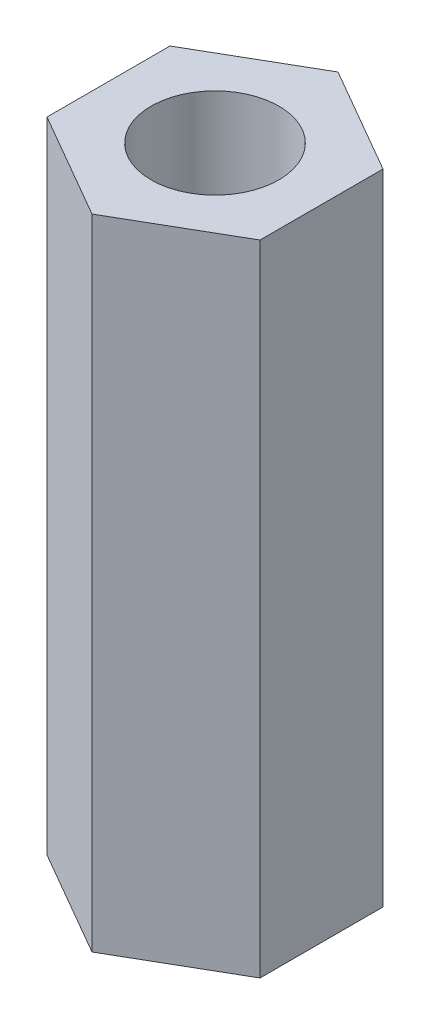
SolidWorks part; units mm, degrees
ref_plane "Piano frontale" through (0, 0, 0) normal (0, 0, 1) x (1, 0, 0)
ref_plane "Piano superiore" through (0, 0, 0) normal (0, 1, 0) x (1, 0, 0)
ref_plane "Piano destro" through (0, 0, 0) normal (1, 0, 0) x (0, 0, -1)
sketch "Sketch1" plane through (0, 0, 0) normal (0, 1, 0) x (1, 0, 0)
  line L1 (-34.9518, 17.0938) -> (-37.4518, 15.6504)
  line L2 (-37.4518, 15.6504) -> (-37.4518, 12.7637)
  line L3 (-37.4518, 12.7637) -> (-34.9518, 11.3203)
  line L4 (-34.9518, 11.3203) -> (-32.4518, 12.7637)
  line L5 (-32.4518, 12.7637) -> (-32.4518, 15.6504)
  line L6 (-32.4518, 15.6504) -> (-34.9518, 17.0938)
  circle A0 centre (-34.9518, 14.207) radius 2.5 construction
  circle A1 centre (-34.9518, 14.207) radius 1.5
  dimension "D1" = 3
  dimension "D2" = 5
extrude "Boss-Extrude1" add sketch "Sketch1" along normal blind 15
